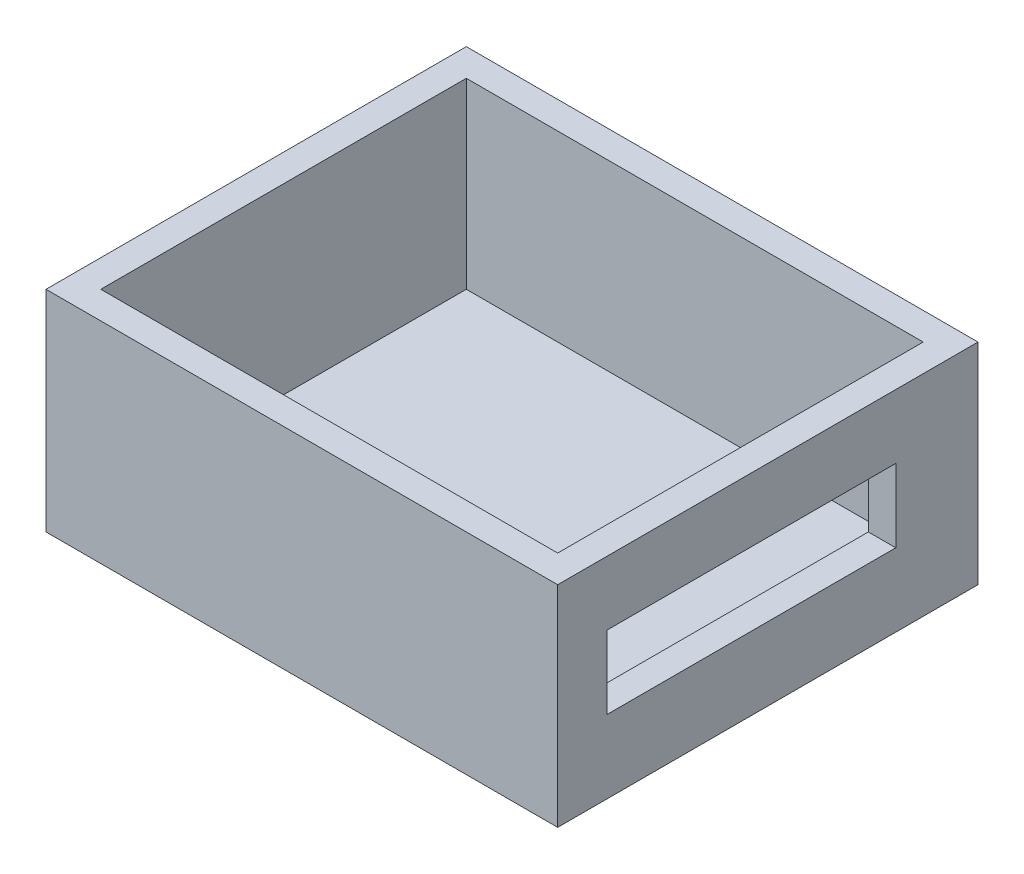
SolidWorks part; units mm, degrees
ref_plane "Front" through (0, 0, 0) normal (0, 0, 1) x (1, 0, 0)
ref_plane "Top" through (0, 0, 0) normal (0, 1, 0) x (1, 0, 0)
ref_plane "Right" through (0, 0, 0) normal (1, 0, 0) x (0, 0, -1)
sketch "Sketch1" plane through (0, 0, 0) normal (0, 1, 0) x (1, 0, 0)
  line L1 (0, 0) -> (25, 0)
  line L2 (0, 0) -> (0, 20)
  line L3 (0, 20) -> (25, 20)
  line L4 (25, 0) -> (25, 20)
  line L5 (0, 0) -> (25, 20) construction
  line L6 (0, 20) -> (25, 0) construction
  point P4 (12.5, 10)
  dimension "D1" = 25
  dimension "D2" = 20
extrude "Boss-Extrude1" add sketch "Sketch1" along normal blind 1.5
sketch "Sketch2" plane through (0, 0, 0) normal (0, -1, 0) x (1, 0, 0)
  line L8 (-1.5, 1.5) -> (-1.5, -21.5)
  line L9 (-1.5, -21.5) -> (26.5, -21.5)
  line L10 (26.5, -21.5) -> (26.5, 1.5)
  line L11 (26.5, 1.5) -> (-1.5, 1.5)
  line L12 (-1.5, 1.5) -> (-1.5, -21.5)
  line L13 (-1.5, -21.5) -> (26.5, -21.5)
  line L14 (26.5, -21.5) -> (26.5, 1.5)
  line L15 (26.5, 1.5) -> (-1.5, 1.5)
  line L16 (0, 0) -> (0, -20)
  line L17 (0, -20) -> (25, -20)
  line L18 (25, -20) -> (25, 0)
  line L19 (25, 0) -> (0, 0)
  line L20 (0, 0) -> (0, -20)
  line L21 (0, -20) -> (25, -20)
  line L22 (25, -20) -> (25, 0)
  line L23 (25, 0) -> (0, 0)
  dimension "D1" = 1.5
  dimension "D2" = 0
extrude "Boss-Extrude2" add sketch "Sketch2" against normal blind 11.5
sketch "Sketch3" plane through (25, 0, 0) normal (-1, 0, 0) x (0, 0, 1)
  line L0 (-20, 11.5) -> (-20, 1.5) construction
  line L1 (-17, 8) -> (-1.2, 8)
  line L2 (-17, 8) -> (-17, 4)
  line L3 (-17, 4) -> (-1.2, 4)
  line L4 (-1.2, 8) -> (-1.2, 4)
  line L5 (-17, 8) -> (-1.2, 4) construction
  line L6 (-17, 4) -> (-1.2, 8) construction
  line L7 (0, 11.5) -> (0, 1.5) construction
  line L8 (0, 1.5) -> (-20, 1.5) construction
  point P0 (-9.1, 6)
  dimension "D1" = 3
  dimension "D2" = 1.2
  dimension "D3" = 2.5
  dimension "D4" = 4
extrude "Cut-Extrude1" cut sketch "Sketch3" against normal blind 10
